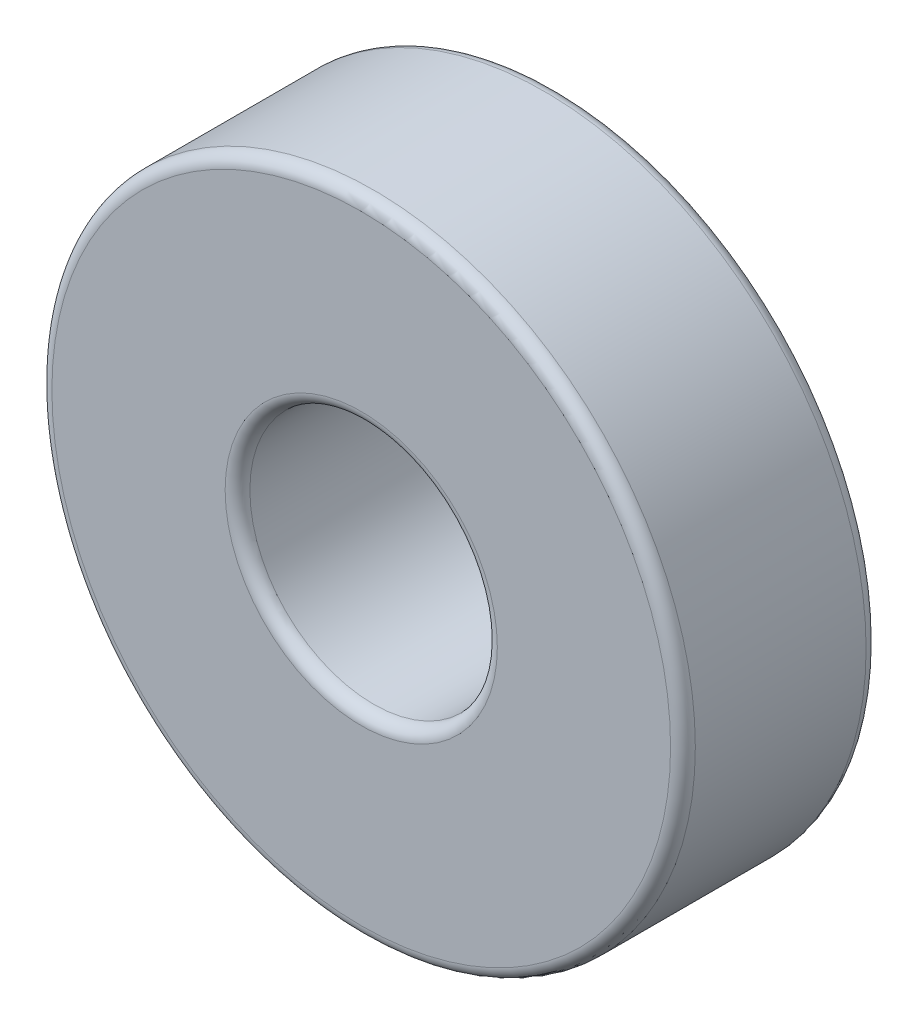
SolidWorks part; units mm, degrees
ref_plane "Front Plane" through (0, 0, 0) normal (0, 0, 1) x (1, 0, 0)
ref_plane "Top Plane" through (0, 0, 0) normal (0, 1, 0) x (1, 0, 0)
ref_plane "Right Plane" through (0, 0, 0) normal (1, 0, 0) x (0, 0, -1)
sketch "Sketch1" plane through (0, 0, 0) normal (0, 0, 1) x (1, 0, 0)
  circle A0 centre (0, 0) radius 5
  circle A1 centre (0, 0) radius 13
  dimension "D1" = 26
  dimension "D2" = 10
extrude "Boss-Extrude1" add sketch "Sketch1" along normal blind 7.9
fillet "Fillet1" radius 0.5 4 edges at (5, 0, 0) (5, 0, 7.9) (13, 0, 0) (13, 0, 7.9)
